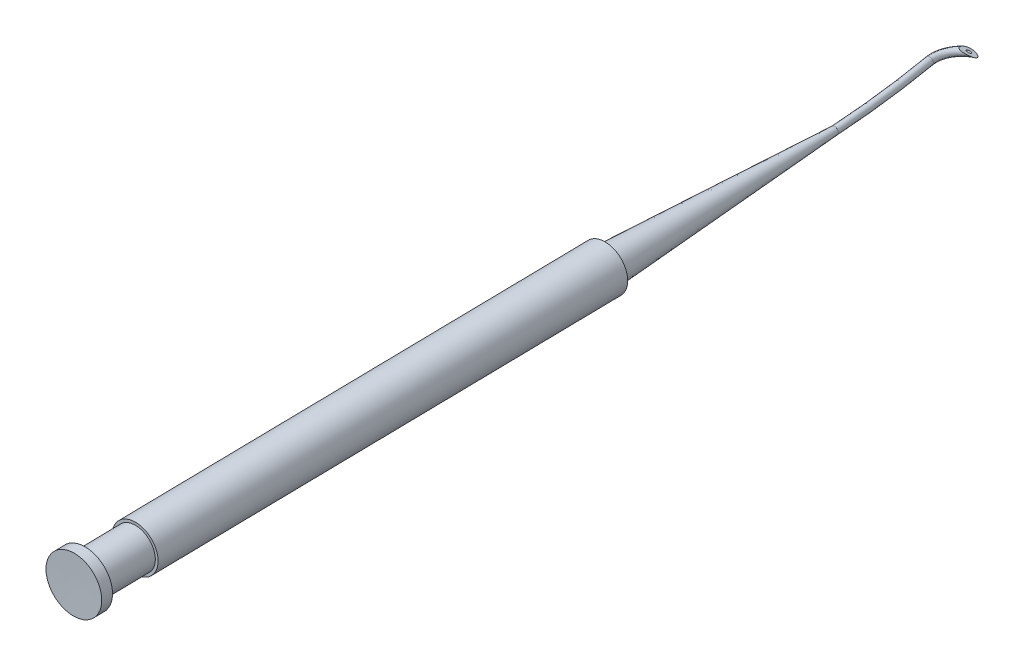
SolidWorks part; units mm, degrees
ref_plane "Front Plane" through (0, 0, 0) normal (0, 0, 1) x (1, 0, 0)
ref_plane "Top Plane" through (0, 0, 0) normal (0, 1, 0) x (1, 0, 0)
ref_plane "Right Plane" through (0, 0, 0) normal (1, 0, 0) x (0, 0, -1)
sketch "linear trace" plane through (0, 0, 0) normal (0, 1, 0) x (1, 0, 0)
  line L0 (160, 640) -> (800, 640) construction
  line L1 (24.3375, 49.7918) -> (24.8861, 17.0058)
  line L2 (24.8861, 17.0058) -> (26.1074, -55.9837)
  line L3 (25.1593, 43.7784) -> (27.244, 18.0728) construction
  line L4 (23.9729, 43.7784) -> (22.4925, 18.0728) construction
  line L5 (22.4925, 18.0728) -> (27.244, 18.0728) construction
  arc A0 (24.9673, 68.7253) -> (22.583, 64.5017) centre (26.347, 65.1616) ccw
  arc A1 (22.583, 64.5017) -> (24.3375, 49.7918) centre (-110.4989, 41.1687) cw
  point P13 (24.8682, 18.0728)
sketch "Sketch2" plane through (0, 0, 0) normal (0, 1, 0) x (1, 0, 0)
  line L0 (24.8861, 17.0058) -> (26.1074, -55.9837) construction
  line L1 (24.3375, 49.7918) -> (24.8861, 17.0058) construction
  line L2 (24.8861, 17.0058) -> (26.1074, -55.9837)
  line L3 (24.3375, 49.7918) -> (24.8861, 17.0058)
  line L4 (24.3375, 49.7918) -> (24.8375, 49.7918)
  line L5 (24.8375, 49.7918) -> (27.1636, 17.8476)
  line L6 (27.9725, 17.8476) -> (29.0656, -47.4848)
  line L7 (28.6906, -47.4848) -> (28.8077, -54.4839)
  line L8 (28.8077, -54.4839) -> (29.8329, -54.4839)
  line L9 (29.8329, -54.4839) -> (29.8579, -55.9837)
  line L10 (29.8579, -55.9837) -> (26.1074, -55.9837)
  line L11 (28.6906, -47.4848) -> (29.0656, -47.4848)
  line L12 (27.1636, 17.8476) -> (27.9725, 17.8476)
  dimension "D1" = 3.1
  dimension "D2" = 72.9996
  dimension "D3" = 2.725
  dimension "D4" = 3.75
  dimension "D5" = 1.5
  dimension "D6" = 7
  dimension "D7" = 0.5
revolve "Revolve4" add sketch "Sketch2" angle 360 about L2
sketch "Sketch4" plane through (0, 0, 0) normal (0, 1, 0) x (1, 0, 0)
  line L0 (23.8378, 49.775) -> (24.8375, 49.7918) construction
  line L1 (23.8378, 49.775) -> (24.8375, 49.7918) construction
  arc A0 (24.3375, 49.7918) -> (22.583, 64.5017) centre (-110.4989, 41.1687) ccw construction
  arc A1 (24.9673, 68.7253) -> (22.583, 64.5017) centre (26.347, 65.1616) ccw construction
  arc A2 (24.3375, 49.7918) -> (22.583, 64.5017) centre (-110.4989, 41.1687) ccw
  arc A3 (24.9673, 68.7253) -> (22.583, 64.5017) centre (26.347, 65.1616) ccw
ref_plane "Plane1" through (0, 0, -49.7918) normal (0, 0, -1) x (-1, 0, 0)
sketch "Sketch5" plane through (0, 0, -49.7918) normal (0, 0, -1) x (-1, 0, 0)
  circle A0 centre (-24.3376, 0) radius 0.15
  ellipse E0 centre (-24.3376, 0) end of major axis (-24.3376, -0.4999) minor radius 0.4999 construction
  ellipse E1 centre (-24.3376, 0) end of major axis (-24.3376, -0.4999) minor radius 0.4999
  dimension "D1" = 0.3
sweep "Sweep1" add profiles "Sketch5" path "Sketch4"
sketch "Sketch6" plane through (42.4234, 0, -13.3807) normal (0.9537, 0, -0.3008) x (-0.3008, 0, -0.9537)
  line L1 (58.6518, -0.4999) -> (56.562, -0.4999) construction
  ellipse E0 centre (58.0321, 0) end of major axis (58.0321, -0.4999) minor radius 0.4999 construction
ref_plane "Plane3" through (10.3994, 18.887, -3.2801) normal (-0.4768, -0.866, 0.1504) x (0.3008, 0, 0.9537)
sketch "Sketch7" plane through (10.3994, 18.887, -3.2801) normal (-0.4768, -0.866, 0.1504) x (0.3008, 0, 0.9537)
  line L1 (-58.7544, -40.3841) -> (-55.0841, -40.3841)
  line L2 (-58.7544, -40.3841) -> (-58.7544, -34.2828)
  line L3 (-58.7544, -34.2828) -> (-55.0841, -34.2828)
  line L4 (-55.0841, -40.3841) -> (-55.0841, -34.2828)
extrude "Cut-Extrude1" cut sketch "Sketch7" against normal blind 10
equation "\"D1@Sketch5\"=1-0.7"
